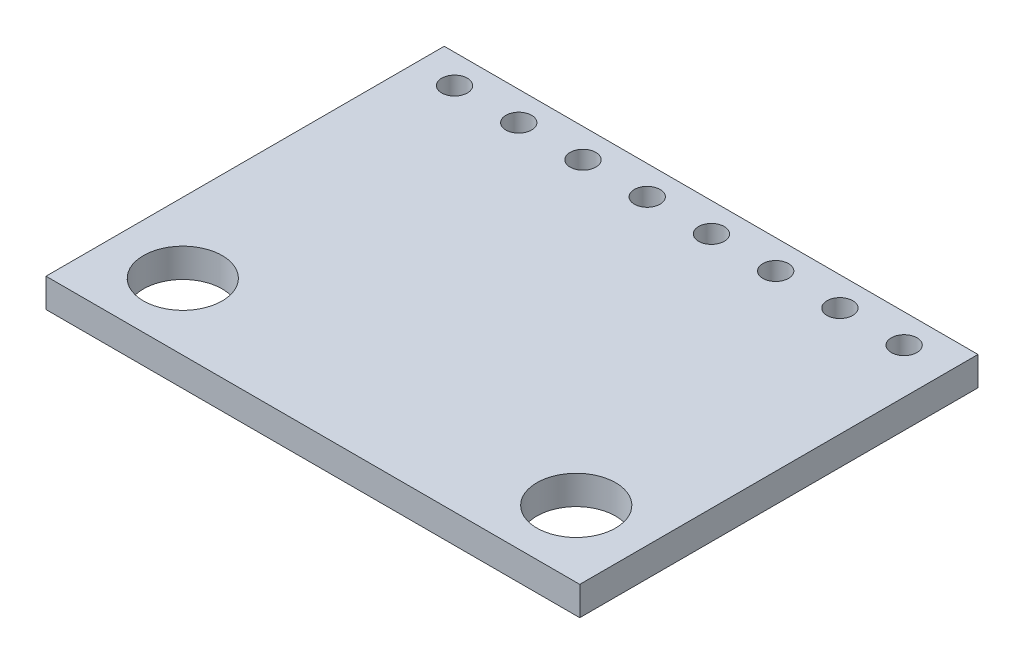
SolidWorks part; units mm, degrees
material "Silicon"
ref_plane "Front Plane" through (0, 0, 0) normal (0, 0, 1) x (1, 0, 0)
ref_plane "Top Plane" through (0, 0, 0) normal (0, 1, 0) x (1, 0, 0)
ref_plane "Right Plane" through (0, 0, 0) normal (1, 0, 0) x (0, 0, -1)
sketch "Sketch1" plane through (0, 0, 0) normal (0, 1, 0) x (1, 0, 0)
  line L0 (0, 0) -> (0, 4.6714) construction
  line L1 (-10.5537, -7.874) -> (10.5537, -7.874)
  line L2 (-10.5537, -7.874) -> (-10.5537, 7.874)
  line L3 (-10.5537, 7.874) -> (10.5537, 7.874)
  line L4 (10.5537, -7.874) -> (10.5537, 7.874)
  line L5 (-10.5537, -7.874) -> (10.5537, 7.874) construction
  line L6 (-10.5537, 7.874) -> (10.5537, -7.874) construction
  circle A0 centre (-7.7787, -5.2387) radius 1.5557
  circle A1 centre (7.7787, -5.2387) radius 1.5557
  circle A2 centre (-9.0043, 6.731) radius 0.508
  circle A3 centre (-6.4643, 6.731) radius 0.508
  circle A4 centre (-3.9243, 6.731) radius 0.508
  circle A5 centre (-1.3843, 6.731) radius 0.508
  circle A6 centre (1.1557, 6.731) radius 0.508
  circle A7 centre (3.6957, 6.731) radius 0.508
  circle A8 centre (6.2357, 6.731) radius 0.508
  circle A9 centre (8.7757, 6.731) radius 0.508
  point P0 (0, 0)
  dimension "D3" = 3.1115
  dimension "D7" = 1.016
  dimension "D1" = 21.1074
  dimension "D2" = 15.748
  dimension "D4" = 2.775
  dimension "D5" = 2.6353
  dimension "D6" = 1.5494
  dimension "D8" = 1.143
  dimension "D9" = 8
extrude "Boss-Extrude1" add sketch "Sketch1" along normal mid plane 1.143
